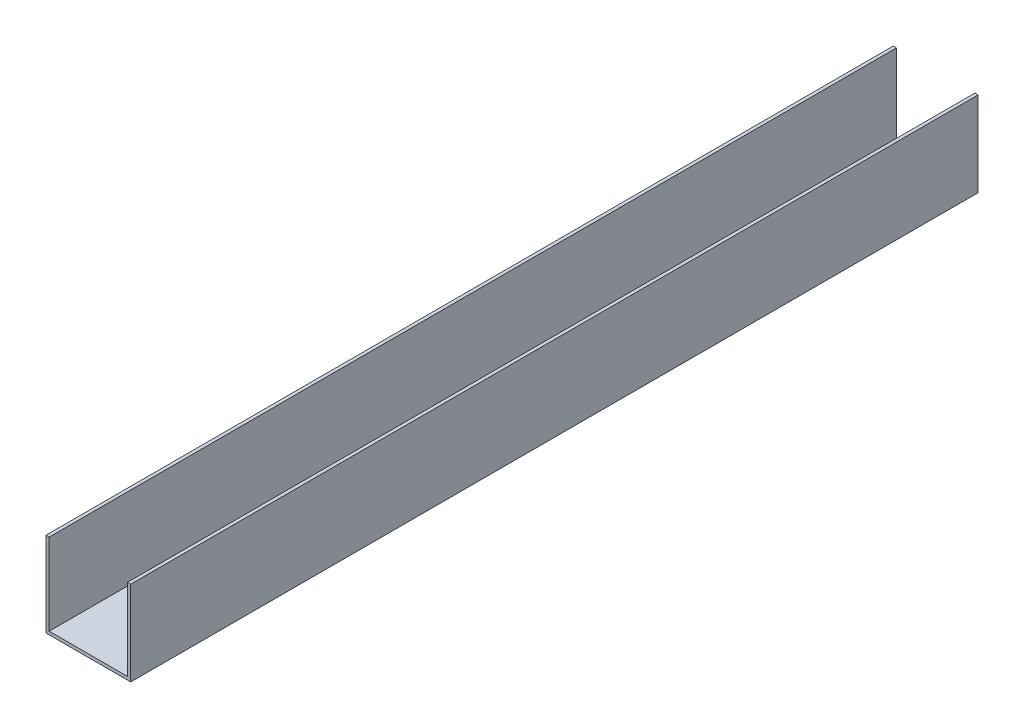
SolidWorks part; units mm, degrees
ref_plane "Alzado" through (0, 0, 0) normal (0, 0, 1) x (1, 0, 0)
ref_plane "Planta" through (0, 0, 0) normal (0, 1, 0) x (1, 0, 0)
ref_plane "Vista lateral" through (0, 0, 0) normal (1, 0, 0) x (0, 0, -1)
ref_plane "Plano1" through (20, 0, 0) normal (1, 0, 0) x (0, 0, -1)
sketch "Croquis1" plane through (20, 0, 0) normal (1, 0, 0) x (0, 0, -1)
  line L0 (0, -1.5) -> (0, 38.5)
  line L1 (0, 38.5) -> (-400, 38.5)
  line L2 (-400, 38.5) -> (-400, -1.5)
  line L3 (-400, -1.5) -> (0, -1.5)
extrude "Saliente-Extruir1" add sketch "Croquis1" against normal blind 40
sketch "Croquis2" plane through (0, 0, 400) normal (0, 0, 1) x (1, 0, 0)
  line L0 (-18.5, 38.5) -> (-18.5, 0)
  line L1 (-18.5, 0) -> (18.5, 0)
  line L2 (18.5, 0) -> (18.5, 38.5)
  line L3 (18.5, 38.5) -> (-18.5, 38.5)
extrude "Cortar-Extruir1" cut sketch "Croquis2" against normal through all
sketch "Croquis3" plane through (0, 0, 0) normal (0, 1, 0) x (-1, 0, 0)
  line L0 (-3.25, 351.5) -> (-3.25, 338.5)
  line L1 (3.25, 338.5) -> (3.25, 351.5)
  arc A0 (3.25, 351.5) -> (-3.25, 351.5) centre (0, 351.5) ccw
  arc A1 (-3.25, 338.5) -> (3.25, 338.5) centre (0, 338.5) ccw
extrude "Cortar-Extruir2" cut sketch "Croquis3" against normal through all
sketch "Croquis4" plane through (0, 0, 0) normal (0, 1, 0) x (-1, 0, 0)
  line L0 (-3.25, 301.5) -> (-3.25, 288.5)
  line L1 (3.25, 288.5) -> (3.25, 301.5)
  arc A0 (3.25, 301.5) -> (-3.25, 301.5) centre (0, 301.5) ccw
  arc A1 (-3.25, 288.5) -> (3.25, 288.5) centre (0, 288.5) ccw
extrude "Cortar-Extruir3" cut sketch "Croquis4" against normal through all
sketch "Croquis5" plane through (0, 0, 0) normal (0, 1, 0) x (-1, 0, 0)
  line L0 (-3.25, 251.5) -> (-3.25, 238.5)
  line L1 (3.25, 238.5) -> (3.25, 251.5)
  arc A0 (3.25, 251.5) -> (-3.25, 251.5) centre (0, 251.5) ccw
  arc A1 (-3.25, 238.5) -> (3.25, 238.5) centre (0, 238.5) ccw
extrude "Cortar-Extruir4" cut sketch "Croquis5" against normal through all
sketch "Croquis6" plane through (0, 0, 0) normal (0, 1, 0) x (-1, 0, 0)
  line L0 (-3.25, 201.5) -> (-3.25, 188.5)
  line L1 (3.25, 188.5) -> (3.25, 201.5)
  arc A0 (3.25, 201.5) -> (-3.25, 201.5) centre (0, 201.5) ccw
  arc A1 (-3.25, 188.5) -> (3.25, 188.5) centre (0, 188.5) ccw
extrude "Cortar-Extruir5" cut sketch "Croquis6" against normal through all
sketch "Croquis7" plane through (0, 0, 0) normal (0, 1, 0) x (-1, 0, 0)
  line L0 (-3.25, 151.5) -> (-3.25, 138.5)
  line L1 (3.25, 138.5) -> (3.25, 151.5)
  arc A0 (3.25, 151.5) -> (-3.25, 151.5) centre (0, 151.5) ccw
  arc A1 (-3.25, 138.5) -> (3.25, 138.5) centre (0, 138.5) ccw
extrude "Cortar-Extruir6" cut sketch "Croquis7" against normal through all
sketch "Croquis8" plane through (0, 0, 0) normal (0, 1, 0) x (-1, 0, 0)
  line L0 (-3.25, 101.5) -> (-3.25, 88.5)
  line L1 (3.25, 88.5) -> (3.25, 101.5)
  arc A0 (3.25, 101.5) -> (-3.25, 101.5) centre (0, 101.5) ccw
  arc A1 (-3.25, 88.5) -> (3.25, 88.5) centre (0, 88.5) ccw
extrude "Cortar-Extruir7" cut sketch "Croquis8" against normal through all
sketch "Croquis9" plane through (0, -1.5, 0) normal (0, -1, 0) x (1, 0, 0)
  line L0 (-3.25, 51.5) -> (-3.25, 38.5)
  line L1 (3.25, 38.5) -> (3.25, 51.5)
  arc A0 (3.25, 51.5) -> (-3.25, 51.5) centre (0, 51.5) ccw
  arc A1 (-3.25, 38.5) -> (3.25, 38.5) centre (0, 38.5) ccw
extrude "Cortar-Extruir8" cut sketch "Croquis9" against normal through all
